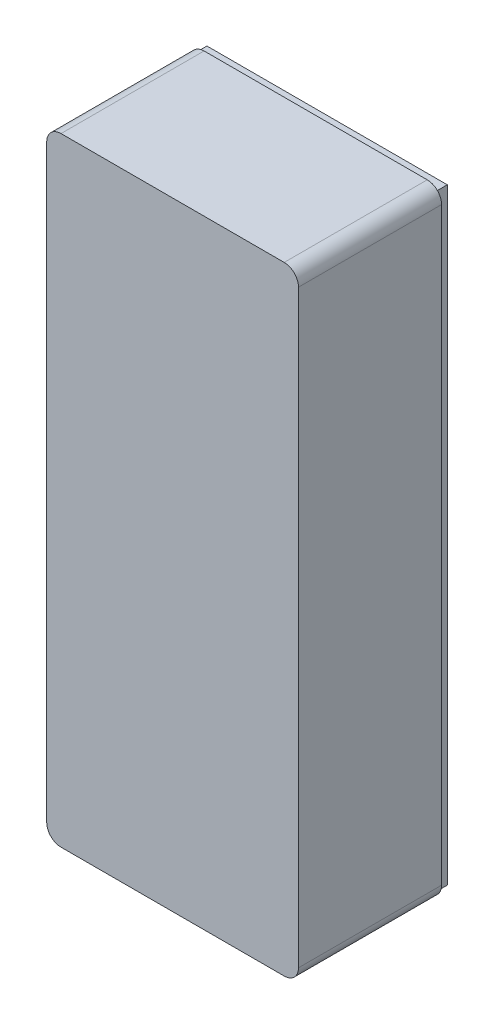
SolidWorks part; units mm, degrees
ref_plane "Přední rovina" through (0, 0, 0) normal (0, 0, 1) x (1, 0, 0)
ref_plane "Horní rovina" through (0, 0, 0) normal (0, 1, 0) x (1, 0, 0)
ref_plane "Pravá rovina" through (0, 0, 0) normal (1, 0, 0) x (0, 0, -1)
sketch "Skica1" plane through (0, 0, 0) normal (0, 0, 1) x (1, 0, 0)
  line L1 (0, 0) -> (44, 0)
  line L2 (0, 0) -> (0, 108)
  line L3 (0, 108) -> (44, 108)
  line L4 (44, 0) -> (44, 108)
  line L5 (2, 2) -> (42, 2)
  line L6 (2, 2) -> (2, 106)
  line L7 (2, 106) -> (42, 106)
  line L8 (42, 2) -> (42, 106)
  point P9 (22, 0)
  dimension "D1" = 108
  dimension "D2" = 44
  dimension "D3" = 2
  dimension "D4" = 2
  dimension "D5" = 2
  dimension "D6" = 2
extrude "Přidat vysunutím1" add sketch "Skica1" along normal blind 25
sketch "Skica2" plane through (0, 0, 25) normal (0, 0, 1) x (1, 0, 0)
  line L1 (0, 108) -> (44, 108)
  line L2 (0, 108) -> (0, 0)
  line L3 (0, 0) -> (44, 0)
  line L4 (44, 108) -> (44, 0)
extrude "Přidat vysunutím2" add sketch "Skica2" along normal blind 2
fillet "Zaoblit1" radius 2.5 4 edges at (0, 108, 13.5) (0, 0, 13.5) (44, 0, 13.5) (44, 108, 13.5)
sketch "Skica3" plane through (0, 0, 0) normal (0, 0, -1) x (-1, 0, 0)
  line L6 (-44, 2.5) -> (-44, 105.5) construction
  line L7 (-43, 107) -> (-1, 107)
  line L8 (-43, 107) -> (-43, 1)
  line L9 (-43, 1) -> (-1, 1)
  line L10 (-1, 107) -> (-1, 1)
  line L11 (0, 105.5) -> (0, 2.5) construction
  line L12 (-2.5, 0) -> (-41.5, 0) construction
  line L13 (-41.5, 108) -> (-2.5, 108) construction
  line L17 (0, 0) -> (-44, 0)
  line L18 (0, 0) -> (0, 108)
  line L19 (0, 108) -> (-44, 108)
  line L20 (-44, 0) -> (-44, 108)
  dimension "D1" = 1
  dimension "D2" = 1
  dimension "D3" = 1
  dimension "D4" = 1
extrude "Odebrat vysunutím1" cut sketch "Skica3" against normal blind 2
sketch "Skica4" plane through (0, 0, 25) normal (0, 0, -1) x (-1, 0, 0)
  line L0 (-42, 2) -> (-42, 10)
  line L9 (-42, 2) -> (-42, 106) construction
  line L10 (-42, 2) -> (-34, 2)
  line L11 (-2, 2) -> (-42, 2) construction
  line L12 (-2, 2) -> (-10, 2)
  line L13 (-2, 2) -> (-2, 10)
  line L14 (-2, 106) -> (-2, 2) construction
  line L15 (-2, 80) -> (-2, 76)
  line L16 (-2, 106) -> (-2, 2) construction
  line L17 (-2, 76) -> (-5, 76)
  line L18 (-2, 80) -> (-2, 84)
  line L19 (-2, 84) -> (-5, 84)
  line L20 (-42, 84) -> (-39, 84)
  line L21 (-42, 2) -> (-42, 106) construction
  line L22 (-42, 84) -> (-42, 76)
  line L23 (-42, 76) -> (-39, 76)
  circle A0 centre (-39, 5) radius 1.5
  circle A1 centre (-5, 5) radius 1.5
  circle A2 centre (-39, 80) radius 1.5
  circle A3 centre (-5, 80) radius 1.5
  arc A4 (-34, 2) -> (-42, 10) centre (-42, 2) ccw
  arc A5 (-2, 10) -> (-10, 2) centre (-2, 2) ccw
  arc A6 (-5, 84) -> (-5, 76) centre (-5, 80) ccw
  arc A7 (-39, 84) -> (-39, 76) centre (-39, 80) cw
  dimension "D2" = 3
  dimension "D5" = 3
  dimension "D4" = 3
  dimension "D6" = 3
  dimension "D7" = 8
  dimension "D9" = 8
  dimension "D10" = 4
  dimension "D1" = 75
  dimension "D3" = 75
  dimension "D8" = 8
  dimension "D11" = 4
extrude "Přidat vysunutím3" add sketch "Skica4" along normal blind 22
sketch "Skica6" plane through (0, 0, 0) normal (0, -1, 0) x (1, 0, 0)
  line L3 (22, 10.4) -> (15.25, 10.4)
  line L4 (15.25, 10.4) -> (15.25, 5)
  line L5 (15.25, 5) -> (28.75, 5)
  line L6 (28.75, 5) -> (28.75, 10.4)
  line L7 (28.75, 10.4) -> (22, 10.4)
  dimension "D3" = 6.75
  dimension "D4" = 13.5
extrude "Odebrat vysunutím2" cut sketch "Skica6" against normal blind 10
sketch "Skica7" plane through (0, 0, 25) normal (0, 0, -1) x (-1, 0, 0)
  line L0 (-42, 16) -> (-2, 16)
  line L1 (-42, 10) -> (-42, 76) construction
  line L2 (-2, 76) -> (-2, 10) construction
  line L3 (-42, 76) -> (-39, 76) construction
  line L4 (-42, 16) -> (-42, 14)
  line L5 (-42, 14) -> (-2, 14)
  line L6 (-2, 14) -> (-2, 16)
  line L7 (-42, 63.683) -> (-37, 63.683)
  line L8 (-37, 63.683) -> (-37, 65.683)
  line L9 (-37, 65.683) -> (-42, 65.683)
  line L10 (-42, 2) -> (-42, 106) construction
  line L11 (-42, 65.683) -> (-42, 63.683)
  dimension "D1" = 60
  dimension "D2" = 2
  dimension "D3" = 5
  dimension "D4" = 2
extrude "Přidat vysunutím4" add sketch "Skica7" along normal blind 10
sketch "Skica8" plane through (0, 0, 0) normal (-1, 0, 0) x (0, 0, 1)
  line L0 (2, 1) -> (2, 107) construction
  line L1 (9.5, 22) -> (15.5, 22)
  line L2 (9.5, 22) -> (9.5, 34)
  line L3 (9.5, 34) -> (15.5, 34)
  line L4 (15.5, 22) -> (15.5, 34)
  line L5 (27, 0) -> (2, 0) construction
  circle A0 centre (12.5, 35.5) radius 0.95
  circle A1 centre (12.5, 20.5) radius 0.95
  point P8 (14.5, 0)
  point P13 (9.5, 28)
  dimension "D5" = 1.9
  dimension "D6" = 1.9
  dimension "D8" = 15
  dimension "D1" = 12
  dimension "D2" = 6
  dimension "D3" = 7.5
  dimension "D4" = 22
  dimension "D7" = 7.5
extrude "Odebrat vysunutím3" cut sketch "Skica8" against normal blind 10
